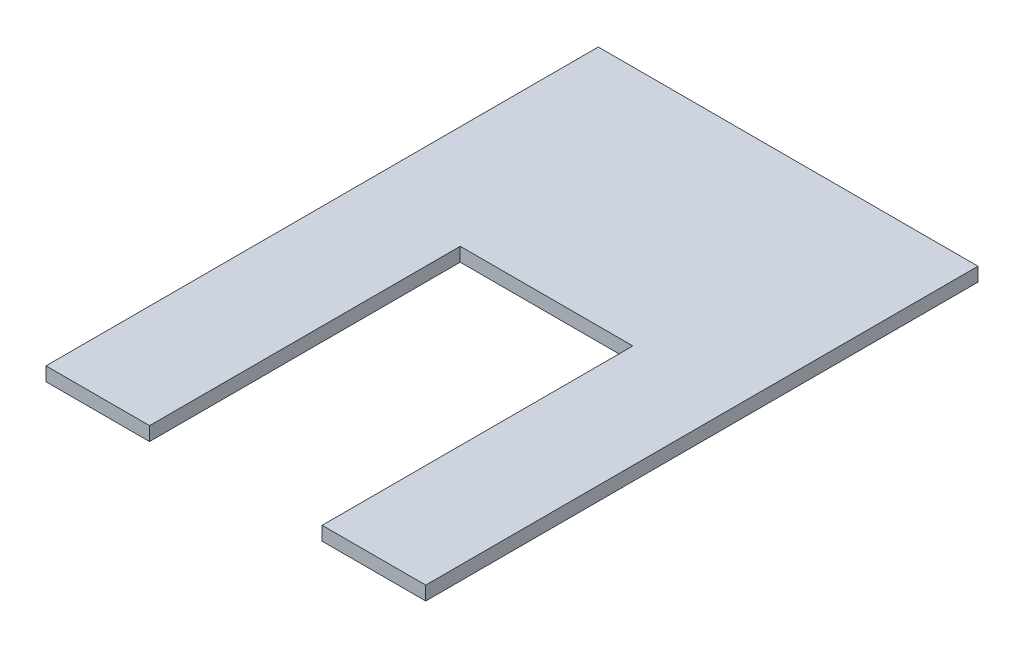
SolidWorks part; units mm, degrees
ref_plane "Front Plane" through (0, 0, 0) normal (0, 0, 1) x (1, 0, 0)
ref_plane "Top Plane" through (0, 0, 0) normal (0, 1, 0) x (1, 0, 0)
ref_plane "Right Plane" through (0, 0, 0) normal (1, 0, 0) x (0, 0, -1)
sketch "Sketch1" plane through (0, 0, 0) normal (0, 1, 0) x (1, 0, 0)
  line L9 (0, 0) -> (69.85, 0)
  line L10 (0, 0) -> (0, 101.6)
  line L11 (0, 101.6) -> (69.85, 101.6)
  line L12 (69.85, 0) -> (69.85, 101.6)
  dimension "D1" = 69.85
  dimension "D2" = 101.6
extrude "Boss-Extrude1" add sketch "Sketch1" along normal blind 2.54
sketch "Sketch2" plane through (0, 2.54, 0) normal (0, 1, 0) x (1, 0, 0)
  line L0 (0, 0) -> (69.85, 0) construction
  line L1 (19.05, 0) -> (50.8, 0)
  line L2 (19.05, 0) -> (19.05, 57.15)
  line L3 (19.05, 57.15) -> (50.8, 57.15)
  line L4 (50.8, 0) -> (50.8, 57.15)
  line L5 (0, 101.6) -> (0, 0) construction
  line L6 (69.85, 0) -> (69.85, 101.6) construction
  dimension "D1" = 19.05
  dimension "D2" = 19.05
  dimension "D3" = 57.15
extrude "Cut-Extrude1" cut sketch "Sketch2" against normal blind 2.54
